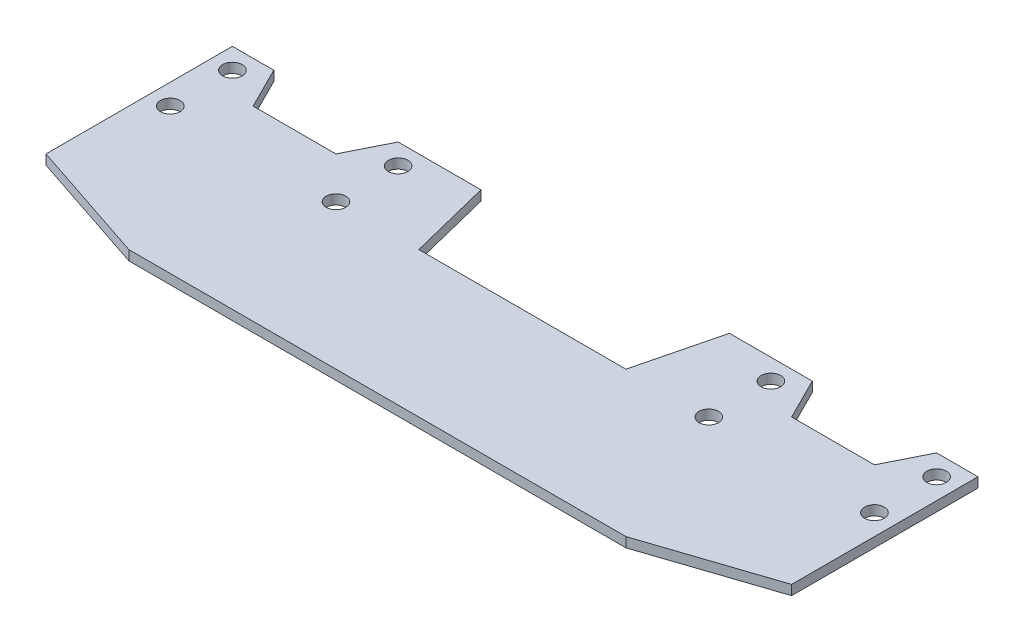
SolidWorks part; units mm, degrees
material "Ti-6Al-4VSolution treated and aged (SS)"
ref_plane "Front Plane" through (0, 0, 0) normal (0, 0, 1) x (1, 0, 0)
ref_plane "Top Plane" through (0, 0, 0) normal (0, 1, 0) x (1, 0, 0)
ref_plane "Right Plane" through (0, 0, 0) normal (1, 0, 0) x (0, 0, -1)
sketch "Sketch1" plane through (0, 0, 0) normal (0, 1, 0) x (1, 0, 0)
  line L0 (-57.15, -11.1125) -> (-38.1, -17.4625)
  line L1 (-38.1, -17.4625) -> (38.1, -17.4625)
  line L2 (-57.15, -11.1125) -> (-57.15, 17.4625)
  line L3 (-57.15, 17.4625) -> (-19.05, 17.4625)
  line L4 (57.15, -11.1125) -> (57.15, 17.4625)
  line L5 (-57.15, -17.4625) -> (57.15, 17.4625) construction
  line L6 (-57.15, 17.4625) -> (57.15, -17.4625) construction
  line L7 (0, 17.4625) -> (0, -17.4625) construction
  line L8 (57.15, -11.1125) -> (38.1, -17.4625)
  line L9 (-57.15, -17.4625) -> (-57.15, -11.1125) construction
  line L10 (-57.15, -17.4625) -> (-38.1, -17.4625) construction
  line L11 (38.1, -17.4625) -> (57.15, -17.4625) construction
  line L12 (57.15, -17.4625) -> (57.15, -11.1125) construction
  line L13 (-19.05, 17.4625) -> (-15.875, 4.7625)
  line L14 (-15.875, 4.7625) -> (15.875, 4.7625)
  line L15 (19.05, 17.4625) -> (15.875, 4.7625)
  line L16 (19.05, 17.4625) -> (57.15, 17.4625)
  line L17 (-19.05, 17.4625) -> (0, 17.4625) construction
  line L18 (0, 17.4625) -> (19.05, 17.4625) construction
  point P0 (0, 0)
  point P16 (0, 4.7625)
  dimension "D1" = 114.3
  dimension "D2" = 34.925
  dimension "D3" = 19.05
  dimension "D4" = 6.35
  dimension "D5" = 38.1
  dimension "D6" = 31.75
  dimension "D7" = 12.7
extrude "Boss-Extrude1" add sketch "Sketch1" along normal blind 1.4985
sketch "Sketch2" plane through (0, 1.4985, 0) normal (0, 1, 0) x (1, 0, 0)
  line L0 (-53.975, 14.2875) -> (-28.575, 14.2875) construction
  line L1 (-19.05, 17.4625) -> (-57.15, 17.4625) construction
  line L3 (-57.15, 17.4625) -> (-57.15, -11.1125) construction
  circle A0 centre (-53.975, 14.2875) radius 1.5
  circle A4 centre (-28.575, 14.2875) radius 1.5
  dimension "D1" = 3
  dimension "D2" = 3.175
  dimension "D3" = 3.175
  dimension "D4" = 25.4
extrude "Cut-Extrude1" cut sketch "Sketch2" against normal through all
sketch "Sketch5" plane through (0, 1.4985, 0) normal (0, 1, 0) x (1, 0, 0)
  line L0 (-50.8, 17.4625) -> (-47.625, 11.1125)
  line L1 (-19.05, 17.4625) -> (-57.15, 17.4625) construction
  line L2 (-47.625, 11.1125) -> (-34.925, 11.1125)
  line L3 (-34.925, 11.1125) -> (-31.75, 17.4625)
  line L4 (-53.975, 14.2875) -> (-50.8, 17.4625) construction
  line L5 (-28.575, 14.2875) -> (-31.75, 17.4625) construction
  line L6 (-50.8, 17.4625) -> (-31.75, 17.4625)
  dimension "D1" = 6.35
  dimension "D2" = 3.175
  dimension "D3" = 3.175
extrude "Cut-Extrude2" cut sketch "Sketch5" against normal through all
pattern_linear "LPattern1" count 2 spacing 9.525 along (0, 0, 1) of "Cut-Extrude1"
mirror "Mirror1" about plane through (0, 0, 0) normal (1, 0, 0) of "LPattern1", "Cut-Extrude2", "Cut-Extrude1"
